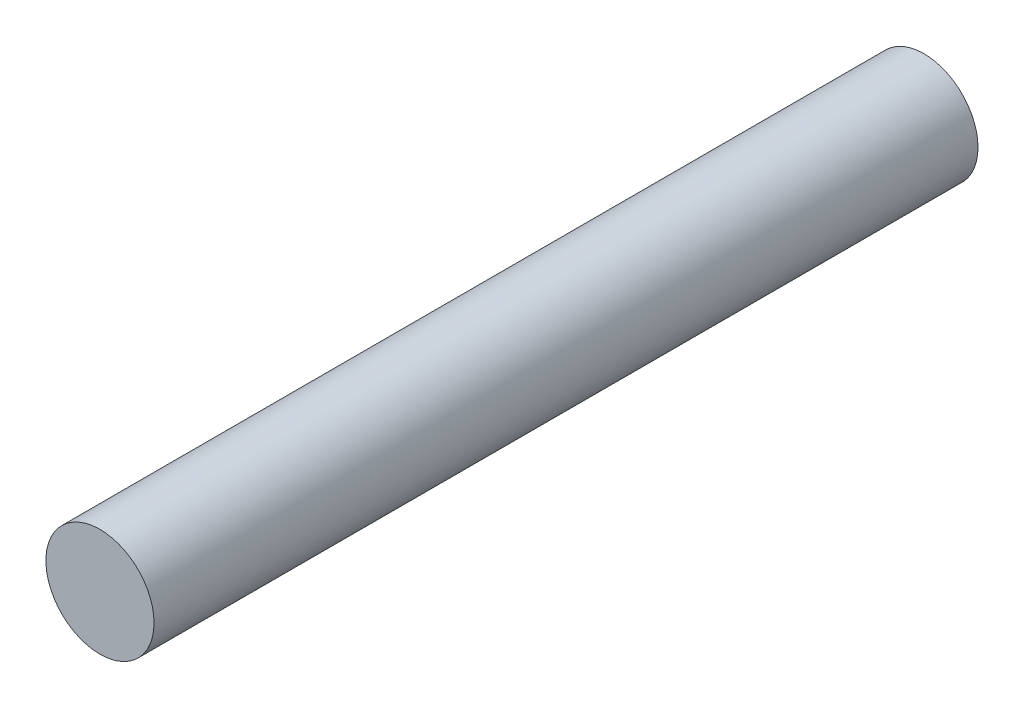
SolidWorks part; units mm, degrees
ref_plane "Front Plane" through (0, 0, 0) normal (0, 0, 1) x (1, 0, 0)
ref_plane "Top Plane" through (0, 0, 0) normal (0, 1, 0) x (1, 0, 0)
ref_plane "Right Plane" through (0, 0, 0) normal (1, 0, 0) x (0, 0, -1)
sketch "Sketch1" plane through (0, 0, 0) normal (0, 0, 1) x (1, 0, 0)
  circle A0 centre (0, 0) radius 2.5
  dimension "D1" = 5
extrude "Boss-Extrude1" add sketch "Sketch1" along normal mid plane 38.1
